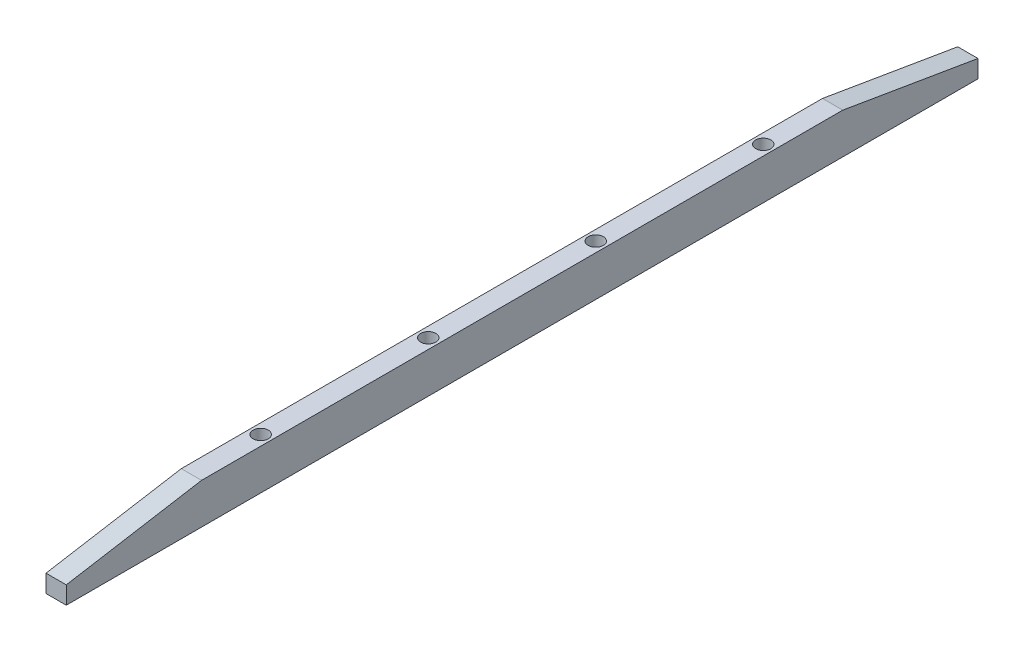
SolidWorks part; units mm, degrees
ref_plane "Front Plane" through (0, 0, 0) normal (0, 0, 1) x (1, 0, 0)
ref_plane "Top Plane" through (0, 0, 0) normal (0, 1, 0) x (1, 0, 0)
ref_plane "Right Plane" through (0, 0, 0) normal (1, 0, 0) x (0, 0, -1)
sketch "Sketch7" plane through (0, 0, 0) normal (1, 0, 0) x (0, 0, -1)
  line L0 (0, 0) -> (211.186, 0) construction
  line L1 (211.186, 0) -> (248.465, 0) construction
  line L2 (0, 0) -> (-37.279, 0) construction
  line L3 (105.593, 0) -> (105.593, 12.7) construction
  line L4 (211.186, 0) -> (0, 0)
  line L5 (0, 0) -> (-37.279, 0)
  line L6 (-37.279, 0) -> (-37.279, 5.5333)
  line L7 (5.1167, 12.7) -> (206.0693, 12.7)
  line L8 (206.0693, 12.7) -> (248.465, 5.5333)
  line L9 (248.465, 0) -> (211.186, 0)
  line L10 (-37.279, 5.5333) -> (5.1167, 12.7)
  line L11 (248.465, 5.5333) -> (248.465, 0)
extrude "Boss-Extrude2" add sketch "Sketch7" along normal blind 6.35 separate body
sketch "Sketch8" plane through (0, 0, 0) normal (0, -1, 0) x (1, 0, 0)
  line L0 (3.175, 37.279) -> (3.175, -248.465) construction
  line L1 (6.35, 37.279) -> (0, 37.279) construction
  line L2 (6.35, -248.465) -> (0, -248.465) construction
  circle A0 centre (3.175, -26.843) radius 2.3813
  circle A1 centre (3.175, -79.343) radius 2.3813
  circle A2 centre (3.175, -131.843) radius 2.3813
  circle A3 centre (3.175, -184.343) radius 2.3813
extrude "Cut-Extrude3" cut sketch "Sketch8" against normal blind 12.7
